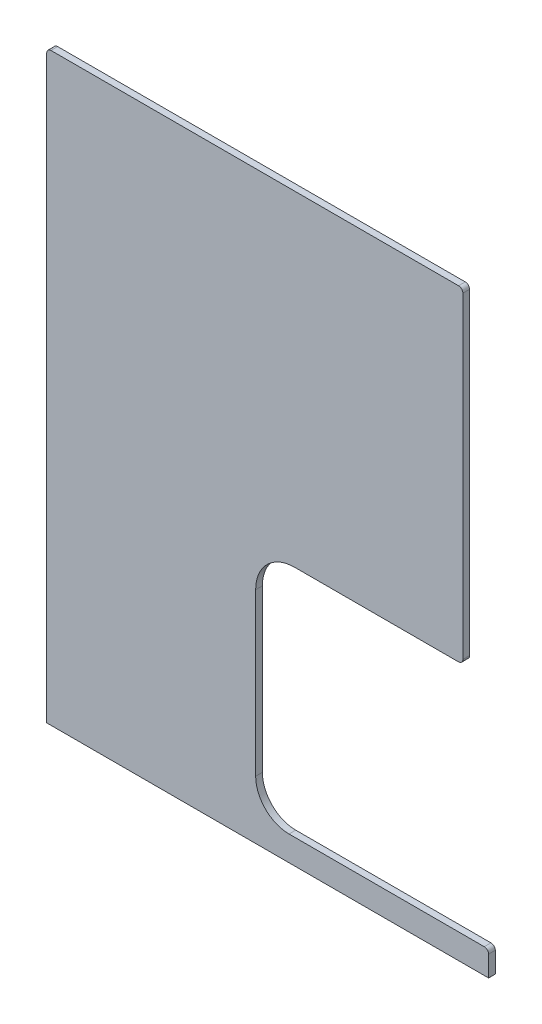
SolidWorks part; units mm, degrees
ref_plane "Front Plane" through (0, 0, 0) normal (0, 0, 1) x (1, 0, 0)
ref_plane "Top Plane" through (0, 0, 0) normal (0, 1, 0) x (1, 0, 0)
ref_plane "Right Plane" through (0, 0, 0) normal (1, 0, 0) x (0, 0, -1)
sketch "Sketch1" plane through (0, 0, 0) normal (0, 0, 1) x (1, 0, 0)
  line L0 (0, 0) -> (0, 744.5)
  line L1 (5.5, 750) -> (528.5, 750)
  line L2 (534, 744.5) -> (534, 337.5)
  line L3 (528.5, 332) -> (318.1, 332)
  line L4 (0, 0) -> (567, 0)
  line L5 (567, 0) -> (567, 26.5)
  line L6 (561.5, 32) -> (313, 32)
  line L9 (313, 32) -> (310.9, 32)
  line L11 (268.1, 282) -> (268.1, 74.8)
  arc A0 (310.9, 32) -> (268.1, 74.8) centre (310.9, 74.8) cw
  arc A1 (318.1, 332) -> (268.1, 282) centre (318.1, 282) ccw
  arc A2 (534, 337.5) -> (528.5, 332) centre (528.5, 337.5) cw
  arc A3 (528.5, 750) -> (534, 744.5) centre (528.5, 744.5) cw
  arc A4 (0, 744.5) -> (5.5, 750) centre (5.5, 744.5) cw
  arc A5 (567, 26.5) -> (561.5, 32) centre (561.5, 26.5) ccw
  point P15 (534, 332)
  point P19 (534, 750)
  point P22 (0, 750)
  point P25 (567, 32)
  dimension "D9" = 207.2
  dimension "D6" = 42.8
  dimension "D10" = 50
  dimension "D11" = 5.5
  dimension "D12" = 5.5
  dimension "D1" = 750
  dimension "D2" = 567
  dimension "D3" = 534
  dimension "D4" = 418
  dimension "D5" = 32
  dimension "D7" = 254
  dimension "D8" = 215.9
extrude "Boss-Extrude1" add sketch "Sketch1" along normal blind 8.6
